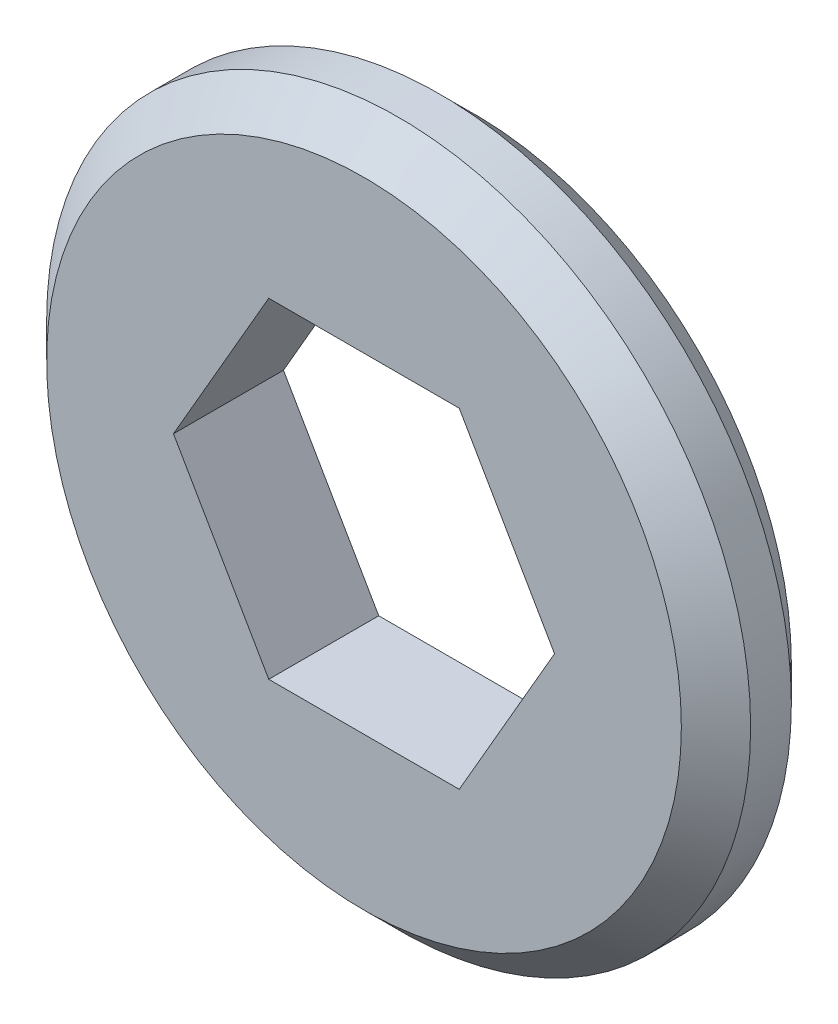
SolidWorks part; units mm, degrees
ref_plane "Front Plane" through (0, 0, 0) normal (0, 0, 1) x (1, 0, 0)
ref_plane "Top Plane" through (0, 0, 0) normal (0, 1, 0) x (1, 0, 0)
ref_plane "Right Plane" through (0, 0, 0) normal (1, 0, 0) x (0, 0, -1)
sketch "Sketch1" plane through (0, 0, 0) normal (0, 0, 1) x (1, 0, 0)
  line L1 (5.4993, 0) -> (2.7496, 4.7625)
  line L2 (2.7496, 4.7625) -> (-2.7496, 4.7625)
  line L3 (-2.7496, 4.7625) -> (-5.4993, 0)
  line L4 (-5.4993, 0) -> (-2.7496, -4.7625)
  line L5 (-2.7496, -4.7625) -> (2.7496, -4.7625)
  line L6 (2.7496, -4.7625) -> (5.4993, 0)
  circle A0 centre (0, 0) radius 10.16
  circle A1 centre (0, 0) radius 4.7625 construction
  dimension "D1" = 20.32
extrude "Boss-Extrude1" add sketch "Sketch1" along normal blind 3.175
chamfer "Chamfer1" distance 1 angle 45 2 edges at (10.16, 0, 0) (10.16, 0, 3.175)
